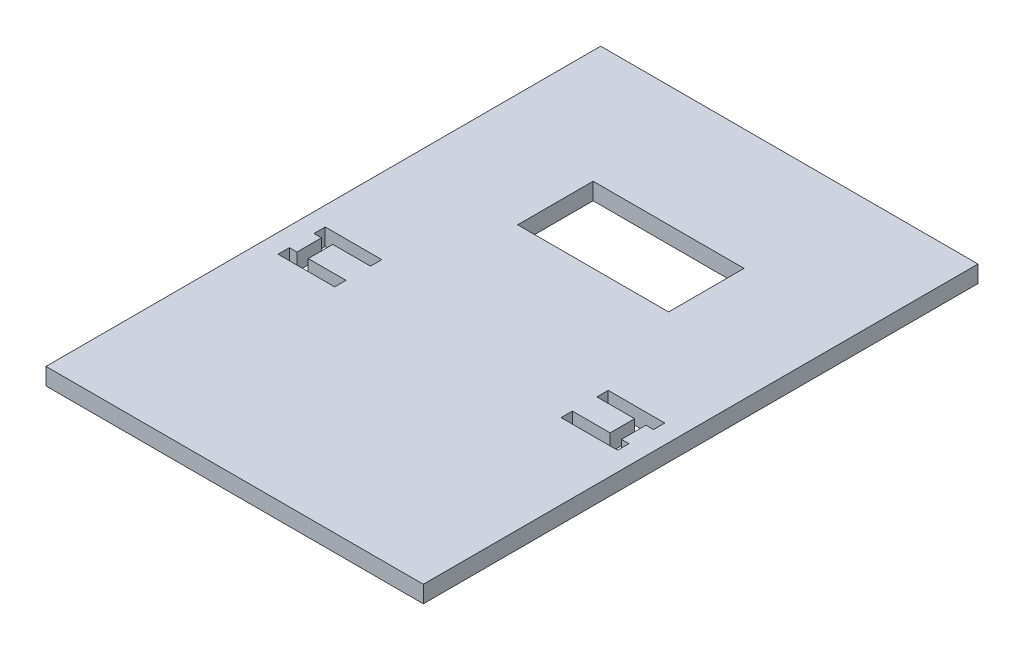
SolidWorks part; units mm, degrees
material "Teak"
ref_plane "Front Plane" through (0, 0, 0) normal (0, 0, 1) x (1, 0, 0)
ref_plane "Top Plane" through (0, 0, 0) normal (0, 1, 0) x (1, 0, 0)
ref_plane "Right Plane" through (0, 0, 0) normal (1, 0, 0) x (0, 0, -1)
sketch "Sketch1" plane through (0, 0, 0) normal (0, 1, 0) x (1, 0, 0)
  line L0 (-20, 19.0292) -> (-20, 39.0292) construction
  line L1 (-20, 39.0292) -> (20, 39.0292) construction
  line L2 (20, 39.0292) -> (20, 19.0292) construction
  line L3 (20, 19.0292) -> (-20, 19.0292) construction
  line L4 (50, 71.0292) -> (50, -75.9708) construction
  line L5 (-50, -75.9708) -> (-50, 71.0292) construction
  line L6 (50, -75.9708) -> (-50, -75.9708) construction
  line L7 (50, 71.0292) -> (-50, 71.0292) construction
  line L8 (-30, -19.4708) -> (-40, -19.4708) construction
  line L9 (-40, -6.9708) -> (-30, -6.9708) construction
  line L10 (-30, -6.9708) -> (-30, -9.9708) construction
  line L11 (-30, -16.4708) -> (-30, -19.4708) construction
  line L12 (30, -19.4708) -> (30, -16.4708) construction
  line L13 (30, -9.9708) -> (30, -6.9708) construction
  line L14 (-40, -6.9708) -> (-45, -6.9708) construction
  line L15 (-45, -6.9708) -> (-45, -9.9708) construction
  line L16 (-45, -9.9708) -> (-43, -9.9708) construction
  line L17 (-43, -16.4708) -> (-45, -16.4708) construction
  line L18 (-45, -16.4708) -> (-45, -19.4708) construction
  line L19 (-45, -19.4708) -> (-40, -19.4708) construction
  line L20 (30, -19.4708) -> (40, -19.4708) construction
  line L21 (40, -6.9708) -> (30, -6.9708) construction
  line L22 (40, -6.9708) -> (45, -6.9708) construction
  line L23 (45, -6.9708) -> (45, -9.9708) construction
  line L24 (45, -9.9708) -> (43, -9.9708) construction
  line L25 (43, -16.4708) -> (45, -16.4708) construction
  line L26 (45, -16.4708) -> (45, -19.4708) construction
  line L27 (45, -19.4708) -> (40, -19.4708) construction
  line L28 (-43, -9.9708) -> (-43, -16.4708) construction
  line L29 (43, -9.9708) -> (43, -16.4708) construction
  line L30 (-40, -9.9708) -> (-40, -16.4708) construction
  line L31 (-40, -16.4708) -> (-30, -16.4708) construction
  line L32 (-40, -9.9708) -> (-30, -9.9708) construction
  line L33 (40, -9.9708) -> (40, -16.4708) construction
  line L34 (40, -16.4708) -> (30, -16.4708) construction
  line L35 (40, -9.9708) -> (30, -9.9708) construction
sketch "Sketch2" plane through (0, 0, 0) normal (0, 1, 0) x (1, 0, 0)
  line L0 (50, -75.9708) -> (-50, -75.9708) construction
  line L1 (50, 71.0292) -> (50, -75.9708) construction
  line L2 (20, 39.0292) -> (20, 19.0292) construction
  line L3 (20, 19.0292) -> (-20, 19.0292) construction
  line L4 (-20, 19.0292) -> (-20, 39.0292) construction
  line L5 (-20, 39.0292) -> (20, 39.0292) construction
  line L6 (50, 71.0292) -> (-50, 71.0292) construction
  line L7 (-50, -75.9708) -> (-50, 71.0292) construction
  line L8 (50, -75.9708) -> (-50, -75.9708)
  line L9 (50, 71.0292) -> (50, -75.9708)
  line L10 (20, 39.0292) -> (20, 19.0292)
  line L11 (20, 19.0292) -> (-20, 19.0292)
  line L12 (-20, 19.0292) -> (-20, 39.0292)
  line L13 (-20, 39.0292) -> (20, 39.0292)
  line L14 (50, 71.0292) -> (-50, 71.0292)
  line L15 (-50, -75.9708) -> (-50, 71.0292)
  line L16 (-45, -6.9708) -> (-30, -6.9708)
  line L17 (-30, -6.9708) -> (-30, -9.9708)
  line L18 (-30, -9.9708) -> (-40, -9.9708)
  line L19 (-40, -9.9708) -> (-40, -16.4708)
  line L20 (-40, -16.4708) -> (-30, -16.4708)
  line L21 (-30, -16.4708) -> (-30, -19.4708)
  line L22 (-30, -19.4708) -> (-45, -19.4708)
  line L23 (-45, -19.4708) -> (-45, -16.4708)
  line L24 (-45, -16.4708) -> (-43, -16.4708)
  line L25 (-43, -16.4708) -> (-43, -9.9708)
  line L26 (-43, -9.9708) -> (-45, -9.9708)
  line L27 (-45, -9.9708) -> (-45, -6.9708)
  line L28 (0, 39.0292) -> (0, -75.9708) construction
  line L29 (43, -9.9708) -> (45, -9.9708)
  line L30 (43, -16.4708) -> (43, -9.9708)
  line L31 (45, -16.4708) -> (43, -16.4708)
  line L32 (45, -19.4708) -> (45, -16.4708)
  line L33 (30, -19.4708) -> (45, -19.4708)
  line L34 (30, -16.4708) -> (30, -19.4708)
  line L35 (40, -16.4708) -> (30, -16.4708)
  line L36 (40, -9.9708) -> (40, -16.4708)
  line L37 (30, -9.9708) -> (40, -9.9708)
  line L38 (30, -6.9708) -> (30, -9.9708)
  line L39 (45, -6.9708) -> (30, -6.9708)
  line L40 (45, -9.9708) -> (45, -6.9708)
extrude "Boss-Extrude1" add sketch "Sketch2" along normal blind 4.5
